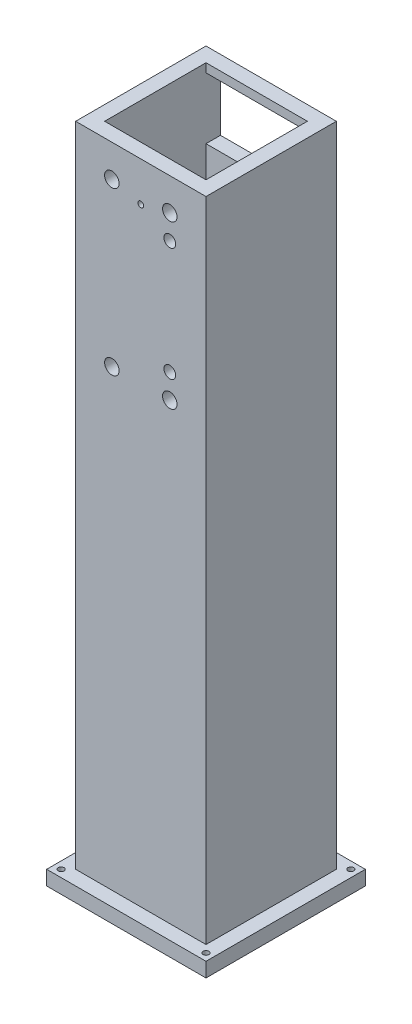
SolidWorks part; units mm, degrees
material "ABS"
ref_plane "Alzado" through (0, 0, 0) normal (0, 0, 1) x (1, 0, 0)
ref_plane "Planta" through (0, 0, 0) normal (0, 1, 0) x (1, 0, 0)
ref_plane "Vista lateral" through (0, 0, 0) normal (1, 0, 0) x (0, 0, -1)
sketch "Croquis1" plane through (0, 0, 0) normal (0, 1, 0) x (1, 0, 0)
  line L1 (-22.5, -22.5) -> (22.5, -22.5)
  line L2 (-22.5, -22.5) -> (-22.5, 22.5)
  line L3 (-22.5, 22.5) -> (22.5, 22.5)
  line L4 (22.5, -22.5) -> (22.5, 22.5)
  line L5 (-22.5, -22.5) -> (22.5, 22.5) construction
  line L6 (-22.5, 22.5) -> (22.5, -22.5) construction
  point P0 (0, 0)
  dimension "D1" = 45
  dimension "D2" = 45
extrude "Saliente-Extruir1" add sketch "Croquis1" along normal blind 300
sketch "Croquis4" plane through (-22.5, 0, 0) normal (-1, 0, 0) x (0, 0, 1)
  line L1 (22.5, 300) -> (22.5, 0) construction
  line L3 (55, 0) -> (-55, 0) construction
  line L5 (4.5, 0) -> (4.5, 34)
  line L6 (4.5, 34) -> (22.5, 34)
  line L8 (22.5, 34) -> (22.5, 0)
  line L9 (22.5, 0) -> (4.5, 0)
  dimension "D4" = 34
extrude "Cortar-Extruir2" cut sketch "Croquis4" against normal through all
sketch "Croquis7" plane through (0, 0, 22.5) normal (0, 0, 1) x (1, 0, 0)
  line L0 (0, -30.25) -> (0, 30.25) construction
  line L1 (-22.5, 246.3879) -> (22.5, 246.3879)
  line L2 (-22.5, 246.3879) -> (-22.5, 273.6121)
  line L3 (-22.5, 273.6121) -> (22.5, 273.6121)
  line L4 (22.5, 246.3879) -> (22.5, 273.6121)
  line L5 (-22.5, 246.3879) -> (22.5, 273.6121) construction
  line L6 (-22.5, 273.6121) -> (22.5, 246.3879) construction
  line L7 (22.5, 300) -> (22.5, 34) construction
  point P0 (0, 260)
  dimension "D1" = 260
sketch "Croquis8" plane through (0, 300, 0) normal (0, 1, 0) x (1, 0, 0)
  line L0 (22.5, -22.5) -> (22.5, 22.5) construction
  line L1 (-17.5, -17.5) -> (17.5, -17.5)
  line L2 (-17.5, -17.5) -> (-17.5, 17.5)
  line L3 (-17.5, 17.5) -> (17.5, 17.5)
  line L4 (17.5, -17.5) -> (17.5, 17.5)
  line L5 (-17.5, -17.5) -> (17.5, 17.5) construction
  line L6 (-17.5, 17.5) -> (17.5, -17.5) construction
  line L7 (22.5, 22.5) -> (-22.5, 22.5) construction
  point P0 (0, 0)
  dimension "D1" = 5
  dimension "D2" = 5
extrude "Cortar-Extruir3" cut sketch "Croquis8" against normal through all contours L3 L4 L1 L2
sketch "Croquis9" plane through (0, 0, -22.5) normal (0, 0, -1) x (-1, 0, 0)
  line L0 (22.5, 273.6121) -> (-22.5, 246.3879) construction
  line L1 (-17.5, 249.4128) -> (17.5, 249.4128)
  line L2 (-17.5, 249.4128) -> (-17.5, 270.5872)
  line L3 (-17.5, 270.5872) -> (17.5, 270.5872)
  line L4 (17.5, 249.4128) -> (17.5, 270.5872)
  line L5 (-17.5, 249.4128) -> (17.5, 270.5872) construction
  line L6 (-17.5, 270.5872) -> (17.5, 249.4128) construction
  line L7 (22.5, 246.3879) -> (22.5, 273.6121) construction
  point P0 (0, 260)
  point P10 (22.5, 260)
  dimension "D1" = 5
extrude "Cortar-Extruir4" cut sketch "Croquis9" against normal blind 10 contours L4 L3 L2 L1
sketch "Croquis10" plane through (0, 0, 22.5) normal (0, 0, 1) x (1, 0, 0)
  circle A0 centre (0, 260) radius 1
  dimension "D1" = 2
extrude "Cortar-Extruir5" cut sketch "Croquis10" against normal blind 10
sketch "Croquis11" plane through (0, 0, 22.5) normal (0, 0, 1) x (1, 0, 0)
  line L0 (22.5, 300) -> (22.5, 34) construction
  line L1 (-22.5, 300) -> (22.5, 300)
  line L2 (-22.5, 300) -> (-22.5, 273.6121)
  line L3 (-22.5, 273.6121) -> (22.5, 273.6121)
  line L4 (22.5, 300) -> (22.5, 273.6121)
  line L5 (-22.5, 273.6121) -> (22.5, 273.6121) construction
  dimension "D1" = 0
extrude "Cortar-Extruir6" cut sketch "Croquis11" against normal through all
sketch "Croquis12" [suppressed] plane through (0, 0, 22.5) normal (0, 0, 1) x (1, 0, 0)
  line L0 (-22.5, 267.3717) -> (22.5, 246.3879)
  line L1 (-22.5, 246.3879) -> (-22.5, 273.6121) construction
  line L2 (-22.5, 246.3879) -> (22.5, 246.3879) construction
  dimension "D1" = 25
sketch "Croquis13" plane through (0, 0, 0) normal (1, 0, 0) x (0, 0, -1)
  line L0 (-22.5, 273.6121) -> (-22.5, 34) construction
  line L1 (-22.5, 50) -> (22.5, 50)
  line L2 (-22.5, 50) -> (-22.5, 0)
  line L3 (-22.5, 0) -> (22.5, 0)
  line L4 (22.5, 50) -> (22.5, 0)
  line L5 (24.75, 0) -> (-24.75, 0) construction
  line L6 (22.5, 273.6121) -> (22.5, 0) construction
  dimension "D1" = 50
extrude "Cortar-Extruir7" cut sketch "Croquis13" against normal through all both and the other way through all
sketch "Croquis14" plane through (0, 50, 0) normal (0, -1, 0) x (1, 0, 0)
  line L1 (-27.5, -27.5) -> (27.5, -27.5)
  line L2 (-27.5, -27.5) -> (-27.5, 27.5)
  line L3 (-27.5, 27.5) -> (27.5, 27.5)
  line L4 (27.5, -27.5) -> (27.5, 27.5)
  line L5 (-27.5, -27.5) -> (27.5, 27.5) construction
  line L6 (-27.5, 27.5) -> (27.5, -27.5) construction
  point P0 (0, 0)
  dimension "D1" = 27.5
  dimension "D2" = 27.5
extrude "Saliente-Extruir2" add sketch "Croquis14" along normal blind 5 contours L3 L4 L1 L2
sketch "Croquis16" plane through (0, 45, 0) normal (0, -1, 0) x (1, 0, 0)
  circle A0 centre (25, 25) radius 1
  circle A1 centre (-25, 25) radius 1
  circle A2 centre (-25, -25) radius 1
  circle A3 centre (25, -25) radius 1
  dimension "D1" = 2
  dimension "D2" = 2.5
  dimension "D3" = 2.5
  dimension "D4" = 2.5
  dimension "D5" = 2.5
extrude "Cortar-Extruir8" cut sketch "Croquis16" against normal through all both
sketch "Croquis17" plane through (0, 0, 22.5) normal (0, 0, 1) x (1, 0, 0)
  line L0 (0, -24.75) -> (0, 24.75) construction
  circle A0 centre (-10, 262.5026) radius 2.5
  circle A3 centre (-10, 206.5026) radius 2.5
  circle A4 centre (10, 262.5026) radius 2.5
  circle A5 centre (10, 206.5026) radius 2.5
  circle A6 centre (10, 254.1026) radius 2.03
  circle A7 centre (10, 214.9026) radius 2.03
  dimension "D1" = 5
  dimension "D3" = 20
  dimension "D4" = 10
  dimension "D7" = 56
extrude "Cortar-Extruir9" cut sketch "Croquis17" against normal through all both and the other way through all
